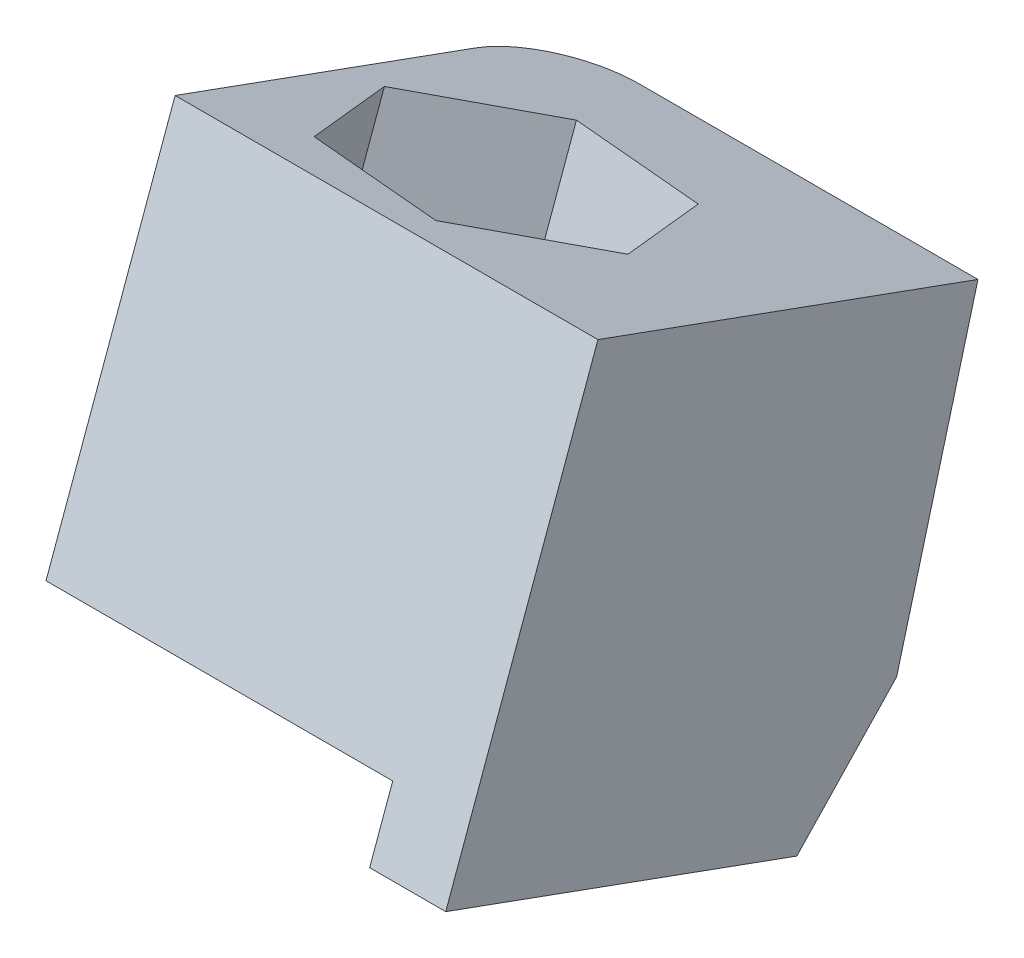
SolidWorks part; units mm, degrees
material "ABS"
ref_plane "Front Plane" through (0, 0, 0) normal (0, 0, 1) x (1, 0, 0)
ref_plane "Top Plane" through (0, 0, 0) normal (0, 1, 0) x (1, 0, 0)
ref_plane "Right Plane" through (0, 0, 0) normal (1, 0, 0) x (0, 0, -1)
sketch "Sketch1" plane through (0, 0, 0) normal (1, 0, 0) x (0, 0, -1)
  line L0 (102.1247, 158.3351) -> (93.8211, 161.3484)
  line L2 (97.42, 171.2656) -> (93.8211, 161.3484)
  line L6 (106.4085, 168.0037) -> (104.4843, 160.8268)
  line L7 (106.5514, 168.537) -> (97.6076, 171.7826) construction
  line L8 (97.42, 171.2656) -> (106.4085, 168.0037)
  line L17 (102.1247, 158.3351) -> (104.4843, 160.8268)
  dimension "D1" = 11.1
  dimension "D2" = 10.55
extrude "Boss-Extrude1" add sketch "Sketch1" along normal blind 10
sketch "Sketch2" plane through (0, 96.4215, -272.7375) normal (0, -0.94, 0.3411) x (1, 0, 0)
  line L0 (5, 190.9213) -> (5, 181.5137) construction
  line L1 (4.0915, 186.3566) -> (4.0915, 186.1335) construction
  line L2 (2.0311, 188.9963) -> (0.7753, 185.8921)
  line L3 (0, 190.3329) -> (10, 190.3329) construction
  line L4 (0.7753, 185.8921) -> (2.8357, 183.2524)
  line L5 (2.8357, 183.2524) -> (6.1519, 183.7169)
  line L6 (6.1519, 183.7169) -> (7.4078, 186.8211)
  line L7 (7.4078, 186.8211) -> (5.3474, 189.4608)
  line L8 (5.3474, 189.4608) -> (2.0311, 188.9963)
  circle A1 centre (4.0915, 186.3566) radius 1.6 construction
  circle A2 centre (4.0915, 186.3566) radius 2.9 construction
  circle A3 centre (4.0915, 186.3566) radius 2.9 construction
extrude "Cut-Extrude1" cut sketch "Sketch2" against normal blind 12
sketch "Sketch3" plane through (0, 172.658, -62.6558) normal (0, -0.94, 0.3411) x (1, 0, 0)
  line L1 (0, -33.1539) -> (8.2, -33.1539)
  line L2 (0, -33.1539) -> (0, -42.7315)
  line L4 (8.2, -33.1539) -> (8.2, -42.7315)
  line L5 (10, -33.1539) -> (10, -41.9874) construction
  line L8 (0, -42.7315) -> (0, -44.6313)
  line L9 (0, -44.6313) -> (8.2, -44.6313)
  line L10 (8.2, -42.7315) -> (8.2, -44.6313)
  dimension "D1" = 1.8
extrude "Cut-Extrude2" cut sketch "Sketch3" against normal blind 1.6
fillet "Fillet1" radius 2 1 edges at (0, 164.4153, -105.4464)
ref_plane "Plane1" through (-1, 0, 0) normal (-1, 0, 0) x (0, 0, 1)
sketch "Sketch5" plane through (0, 174.162, -63.2016) normal (0, -0.94, 0.3411) x (1, 0, 0)
  line L0 (0.7753, -37.5947) -> (7.4078, -36.6657) construction
  line L1 (4.0915, -37.1302) -> (4.0915, -37.3117) construction
  line L2 (0.5412, -33.5623) -> (7.7617, -33.5623)
  line L3 (0.5412, -33.5623) -> (0.5412, -40.2077)
  line L4 (0.5412, -40.2077) -> (7.7617, -40.2077)
  line L5 (7.7617, -33.5623) -> (7.7617, -40.2077)
  circle A0 centre (4.0915, -37.1302) radius 1.6
extrude "Boss-Extrude2" [suppressed] add sketch "Sketch5" against normal blind 0.02
mirror "Mirror6" [suppressed] about plane through (-1, 0, 0) normal (-1, 0, 0)
